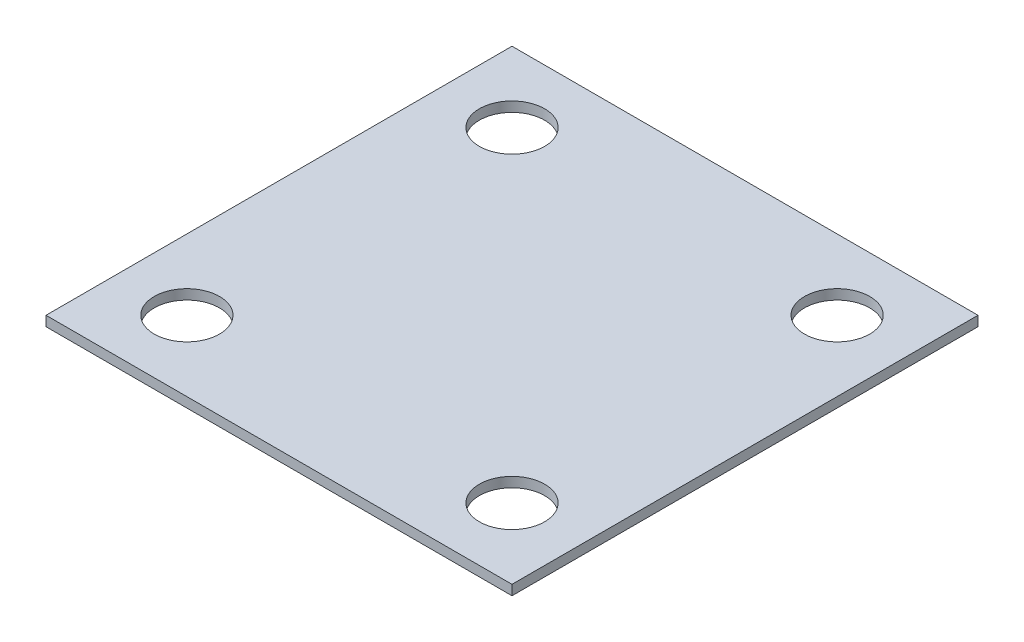
SolidWorks part; units mm, degrees
ref_plane "Front Plane" through (0, 0, 0) normal (0, 0, 1) x (1, 0, 0)
ref_plane "Top Plane" through (0, 0, 0) normal (0, 1, 0) x (1, 0, 0)
ref_plane "Right Plane" through (0, 0, 0) normal (1, 0, 0) x (0, 0, -1)
sketch "Sketch1" plane through (0, 0, 0) normal (0, 1, 0) x (1, 0, 0)
  line L1 (-37.5, -37.5) -> (37.5, -37.5)
  line L2 (-37.5, -37.5) -> (-37.5, 37.5)
  line L3 (-37.5, 37.5) -> (37.5, 37.5)
  line L4 (37.5, -37.5) -> (37.5, 37.5)
  line L5 (-37.5, -37.5) -> (37.5, 37.5) construction
  line L6 (-37.5, 37.5) -> (37.5, -37.5) construction
  circle A0 centre (-26.1629, -26.1629) radius 5.25
  circle A1 centre (26.1631, -26.1629) radius 5.25
  circle A2 centre (-26.1629, 26.1629) radius 5.25
  circle A3 centre (26.1631, 26.1629) radius 5.25
  point P0 (0, 0)
  dimension "D3" = 10.5
  dimension "D7" = 10.5
  dimension "D8" = 10.5
  dimension "D9" = 10.5
  dimension "D4" = 26.1629
  dimension "D6" = 26.1629
  dimension "D2" = 26.1629
  dimension "D1" = 75
  dimension "D5" = 74
extrude "Boss-Extrude1" add sketch "Sketch1" along normal blind 1.6
equation "\"width\"=26.1629"
equation "\"D2@Sketch1\"=\"width\""
equation "\"D6@Sketch1\"=\"width\""
equation "\"D4@Sketch1\"=\"width\""
